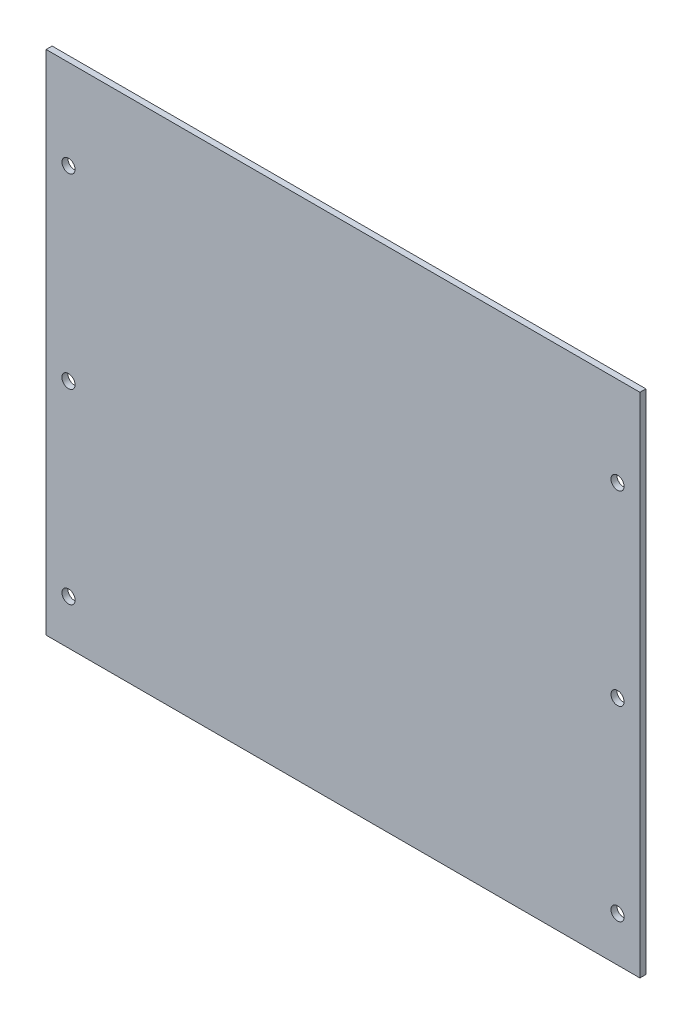
SolidWorks part; units mm, degrees
ref_plane "正面" through (0, 0, 0) normal (0, 0, 1) x (1, 0, 0)
ref_plane "平面" through (0, 0, 0) normal (0, 1, 0) x (1, 0, 0)
ref_plane "右側面" through (0, 0, 0) normal (1, 0, 0) x (0, 0, -1)
sketch "ｽｹｯﾁ1" plane through (0, 0, 0) normal (0, 0, 1) x (1, 0, 0)
  line L1 (-99.5, 85) -> (99.5, 85)
  line L2 (-99.5, 85) -> (-99.5, -85)
  line L3 (-99.5, -85) -> (99.5, -85)
  line L4 (99.5, 85) -> (99.5, -85)
  line L5 (-99.5, 85) -> (99.5, -85) construction
  line L6 (-99.5, -85) -> (99.5, 85) construction
  point P0 (0, 0)
  dimension "D1" = 199
  dimension "D2" = 170
extrude "ﾎﾞｽ - 押し出し1" add sketch "ｽｹｯﾁ1" along normal blind 2
sketch "ｽｹｯﾁ2" plane through (0, 0, 2) normal (0, 0, 1) x (1, 0, 0)
  line L0 (-99.5, -85) -> (-92, -85)
  line L1 (-99.5, -85) -> (99.5, -85) construction
  line L2 (-92, -85) -> (-92, -70)
  line L3 (-92, -85) -> (-92, -7.5)
  line L4 (-92, -7.5) -> (-92, 54.2498)
  line L5 (-92, -85) -> (-92, 55)
  line L6 (99.5, -85) -> (92, -85)
  line L7 (92, -85) -> (92, -70)
  line L8 (92, -85) -> (92, -7.5)
  line L9 (92, -85) -> (92, 55)
  circle A0 centre (-92, -70) radius 2.2
  circle A1 centre (-92, -7.5) radius 2.2
  circle A2 centre (-92, 55) radius 2.2
  circle A3 centre (92, -70) radius 2.2
  circle A4 centre (92, -7.5) radius 2.2
  circle A5 centre (92, 55) radius 2.2
  dimension "D5" = 4.4
  dimension "D6" = 4.4
  dimension "D7" = 4.4
  dimension "D10" = 4.4
  dimension "D12" = 4.4
  dimension "D14" = 4.4
  dimension "D1" = 7.5
  dimension "D2" = 15
  dimension "D3" = 77.5
  dimension "D4" = 140
  dimension "D8" = 7.5
  dimension "D9" = 15
  dimension "D11" = 77.5
  dimension "D13" = 140
extrude "ｶｯﾄ - 押し出し1" cut sketch "ｽｹｯﾁ2" against normal blind 2 contours L4 A2 | L4 A2 | L3 A1 L4 | L4 A1 L3 | L5 A0 L3 | L3 A0 L5 | A5 | A4 | A3
